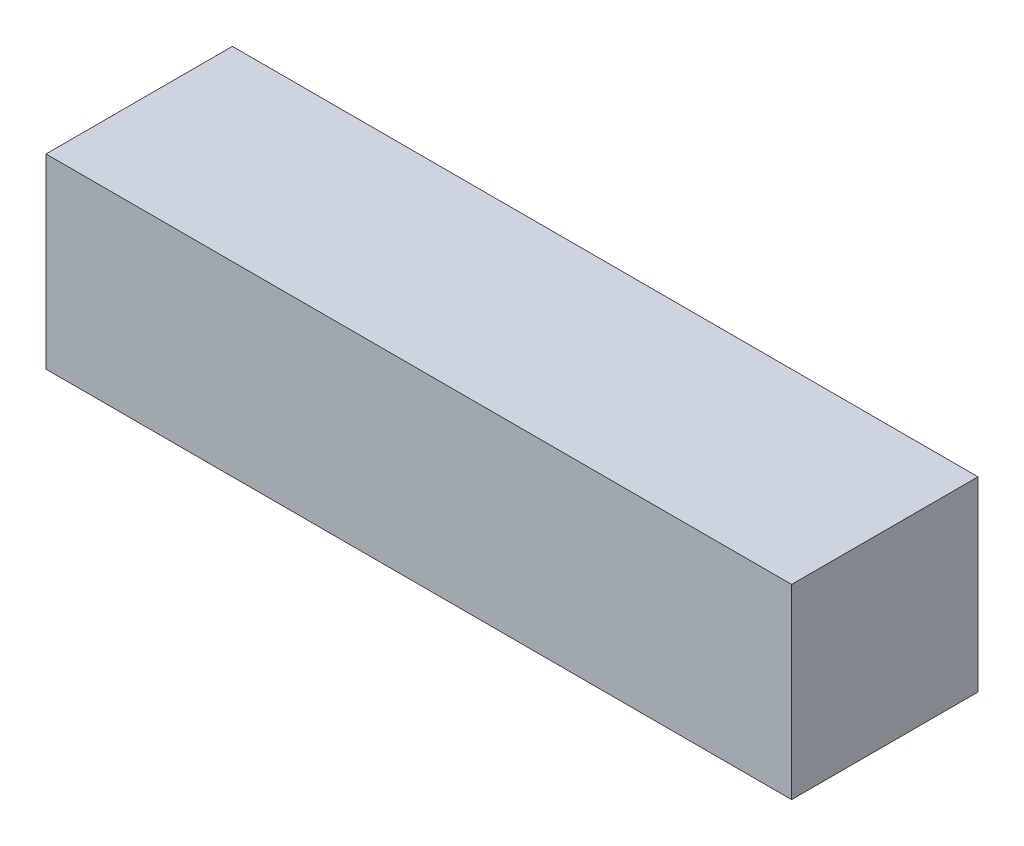
SolidWorks part; units mm, degrees
ref_plane "Front Plane" through (0, 0, 0) normal (0, 0, 1) x (1, 0, 0)
ref_plane "Top Plane" through (0, 0, 0) normal (0, 1, 0) x (1, 0, 0)
ref_plane "Right Plane" through (0, 0, 0) normal (1, 0, 0) x (0, 0, -1)
sketch "Sketch1" plane through (0, 0, 0) normal (0, 0, 1) x (1, 0, 0)
  line L1 (-66.3154, 22.3024) -> (35.2846, 22.3024)
  line L2 (-66.3154, 22.3024) -> (-66.3154, -3.0976)
  line L3 (-66.3154, -3.0976) -> (35.2846, -3.0976)
  line L4 (35.2846, 22.3024) -> (35.2846, -3.0976)
  dimension "D1" = 101.6
  dimension "D2" = 25.4
extrude "Boss-Extrude1" add sketch "Sketch1" along normal blind 25.4
